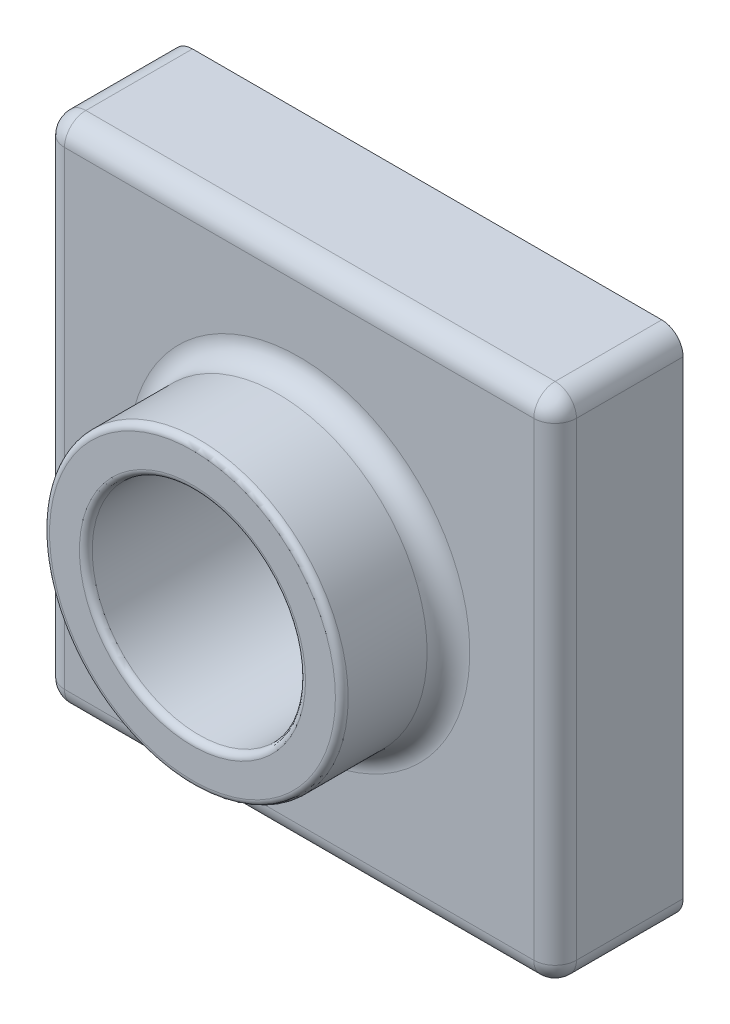
SolidWorks part; units mm, degrees
ref_plane "Front Plane" through (0, 0, 0) normal (0, 0, 1) x (1, 0, 0)
ref_plane "Top Plane" through (0, 0, 0) normal (0, 1, 0) x (1, 0, 0)
ref_plane "Right Plane" through (0, 0, 0) normal (1, 0, 0) x (0, 0, -1)
sketch "Sketch3" plane through (0, 0, 0) normal (0, 0, 1) x (1, 0, 0)
  line L1 (0, 0) -> (120, 0)
  line L2 (0, 0) -> (0, 120)
  line L3 (0, 120) -> (120, 120)
  line L4 (120, 0) -> (120, 120)
  point P5 (194.0828, 120)
  dimension "D1" = 120
  dimension "D2" = 120
extrude "Boss-Extrude1" add sketch "Sketch3" along normal blind 30
sketch "Sketch4" plane through (0, 0, 30) normal (0, 0, 1) x (1, 0, 0)
  line L0 (120, 120) -> (0, 120) construction
  line L1 (0, 120) -> (0, 0) construction
  circle A0 centre (60, 60) radius 35
  dimension "D1" = 70
  dimension "D2" = 60
  dimension "D3" = 60
extrude "Boss-Extrude2" add sketch "Sketch4" along normal blind 25
sketch "Sketch6" plane through (0, 0, 55) normal (0, 0, 1) x (1, 0, 0)
  circle A0 centre (60, 60) radius 25
  dimension "D1" = 50
extrude "Cut-Extrude1" cut sketch "Sketch6" against normal through all
fillet "Fillet3" radius 1.5 2 edges at (95, 60, 55) (85, 60, 55)
fillet "Fillet4" radius 5 4 edges at (0, 0, 15) (120, 0, 15) (0, 120, 15) (120, 120, 15)
fillet "Fillet8" radius 5 9 edges at (1.4645, 118.5355, 30) (60, 120, 30) (118.5355, 118.5355, 30) (120, 60, 30) (118.5355, 1.4645, 30) (60, 0, 30) (1.4645, 1.4645, 30) (0, 60, 30) (95, 60, 30)
shell "Shell1" thickness 2
